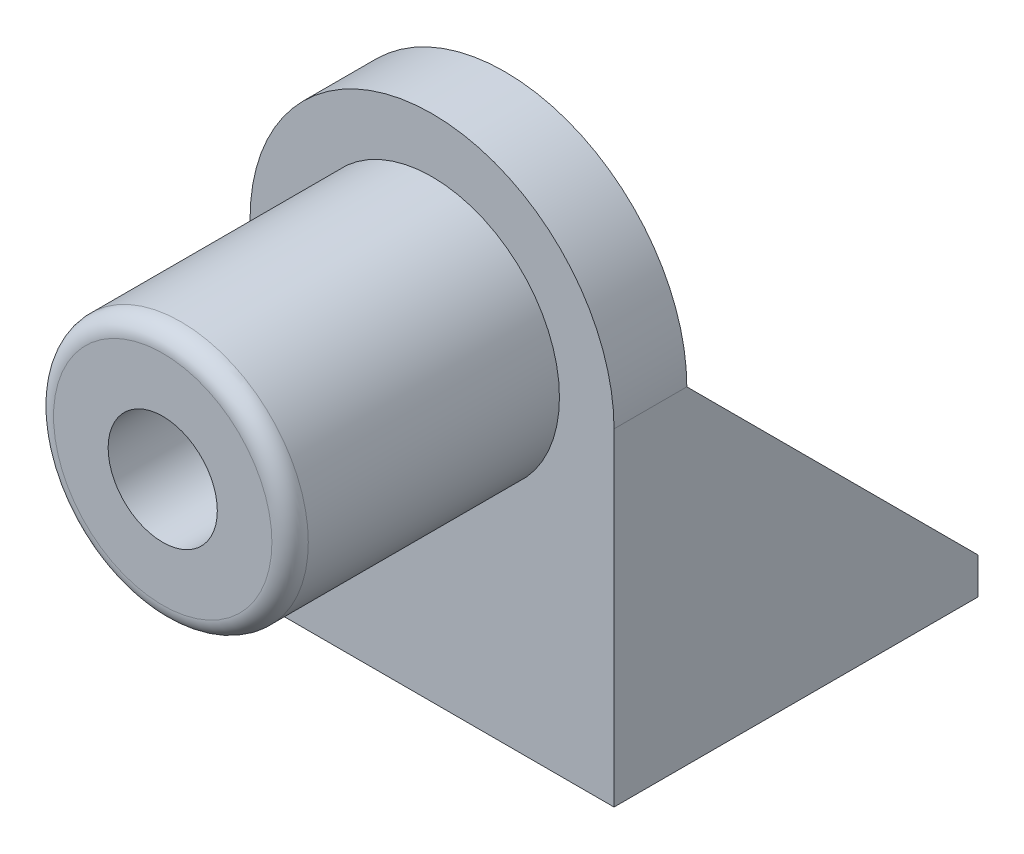
SolidWorks part; units mm, degrees
ref_plane "Front Plane" through (0, 0, 0) normal (0, 0, 1) x (1, 0, 0)
ref_plane "Top Plane" through (0, 0, 0) normal (0, 1, 0) x (1, 0, 0)
ref_plane "Right Plane" through (0, 0, 0) normal (1, 0, 0) x (0, 0, -1)
sketch "Sketch1" plane through (0, 0, 0) normal (0, 0, 1) x (1, 0, 0)
  circle A0 centre (0, 0) radius 11.1125
  circle A1 centre (0, 0) radius 4.7625
  dimension "D1" = 22.225
  dimension "D2" = 9.525
extrude "Boss-Extrude1" add sketch "Sketch1" along normal blind 23.495
sketch "Sketch2" plane through (0, 0, 0) normal (0, 0, -1) x (-1, 0, 0)
  line L0 (-15.875, -28.575) -> (15.875, -28.575) construction
  line L1 (15.875, -28.575) -> (15.875, 0)
  line L2 (-15.875, 0) -> (-15.875, -28.575)
  line L3 (-15.875, -28.575) -> (15.875, -28.575)
  arc A1 (-15.875, 0) -> (15.875, 0) centre (0, 0) cw
  circle A2 centre (0, 0) radius 4.7625 construction
  circle A3 centre (0, 0) radius 4.7625
  point P4 (0, -28.575)
  dimension "D1" = 31.75
  dimension "D2" = 28.575
extrude "Boss-Extrude2" add sketch "Sketch2" along normal blind 6.35
sketch "Sketch3" plane through (0, 0, -6.35) normal (0, 0, -1) x (-1, 0, 0)
  line L0 (15.875, -28.575) -> (15.875, 0) construction
  line L1 (-15.875, -28.575) -> (15.875, -28.575)
  line L2 (-15.875, -28.575) -> (-15.875, -25.4)
  line L3 (-15.875, -25.4) -> (15.875, -25.4)
  line L4 (15.875, -28.575) -> (15.875, -25.4)
  dimension "D1" = 3.175
extrude "Boss-Extrude3" add sketch "Sketch3" along normal blind 25.4
sketch "Sketch4" plane through (-15.875, 0, 0) normal (-1, 0, 0) x (0, 0, 1)
  line L0 (-31.75, -25.4) -> (-6.35, 0)
  line L1 (-6.35, -25.4) -> (-6.35, 0)
  line L2 (-6.35, -25.4) -> (-31.75, -25.4)
extrude "Boss-Extrude4" add sketch "Sketch4" against normal blind 3.175
sketch "Sketch5" plane through (15.875, 0, 0) normal (1, 0, 0) x (0, 0, -1)
  line L0 (6.35, -25.4) -> (31.75, -25.4)
  line L1 (31.75, -25.4) -> (6.35, 0)
  line L2 (6.35, 0) -> (6.35, -25.4)
extrude "Boss-Extrude5" add sketch "Sketch5" against normal blind 3.175
sketch "Sketch6" plane through (0, -25.4, 0) normal (0, 1, 0) x (1, 0, 0)
  line L0 (-12.7, 6.35) -> (12.7, 31.75) construction
  line L2 (-9.525, 9.525) -> (9.525, 9.525) construction
  line L3 (-9.525, 9.525) -> (-9.525, 28.575) construction
  line L4 (-9.525, 28.575) -> (9.525, 28.575) construction
  line L5 (9.525, 9.525) -> (9.525, 28.575) construction
  line L6 (-9.525, 9.525) -> (9.525, 28.575) construction
  line L7 (-9.525, 28.575) -> (9.525, 9.525) construction
  circle A0 centre (-9.525, 28.575) radius 1.5
  circle A1 centre (9.525, 28.575) radius 1.5
  circle A2 centre (9.525, 9.525) radius 1.5
  circle A3 centre (-9.525, 9.525) radius 1.5
  point P4 (0, 19.05)
  dimension "D2" = 3
  dimension "D3" = 3
  dimension "D4" = 3
  dimension "D5" = 3
  dimension "D1" = 19.05
extrude "Cut-Extrude1" cut sketch "Sketch6" against normal blind 12.319
fillet "Fillet1" radius 1.5875 1 edges at (11.1125, 0, 23.495)
